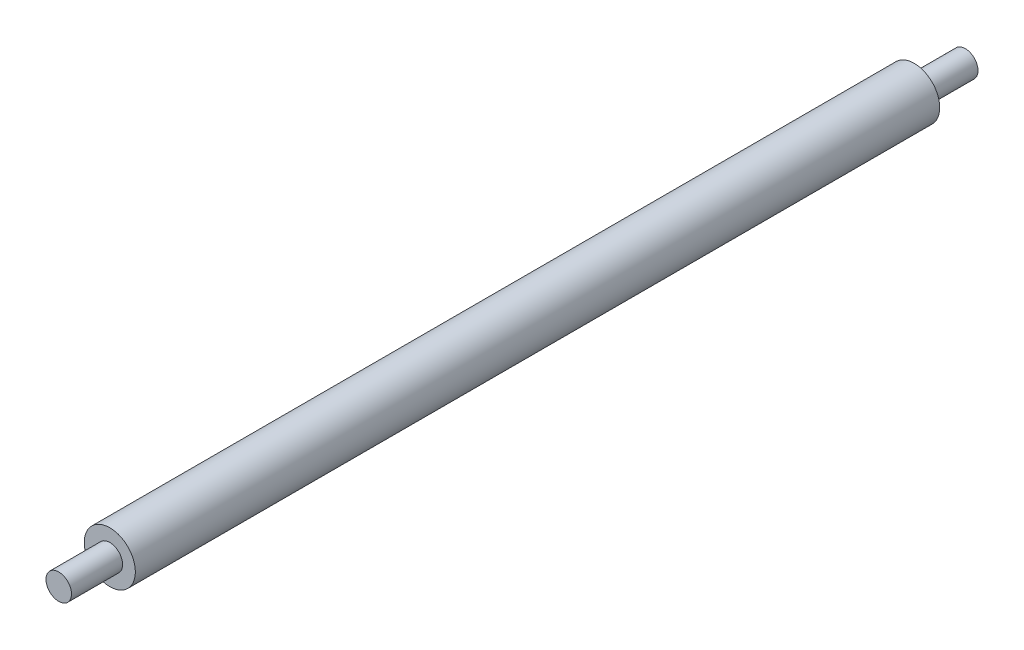
SolidWorks part; units mm, degrees
ref_plane "Front Plane" through (0, 0, 0) normal (0, 0, 1) x (1, 0, 0)
ref_plane "Top Plane" through (0, 0, 0) normal (0, 1, 0) x (1, 0, 0)
ref_plane "Right Plane" through (0, 0, 0) normal (1, 0, 0) x (0, 0, -1)
sketch "Sketch1" plane through (0, 0, 0) normal (0, 0, 1) x (1, 0, 0)
  circle A0 centre (0, 0) radius 10
  dimension "D1" = 20
extrude "Boss-Extrude1" add sketch "Sketch1" along normal blind 315
sketch "Sketch2" plane through (0, 0, 315) normal (0, 0, 1) x (1, 0, 0)
  circle A0 centre (0, 0) radius 5
  dimension "D1" = 10
extrude "Boss-Extrude2" add sketch "Sketch2" along normal blind 20
sketch "Sketch3" plane through (0, 0, 0) normal (0, 0, -1) x (-1, 0, 0)
  circle A0 centre (0, 0) radius 5
  dimension "D1" = 10
extrude "Boss-Extrude3" add sketch "Sketch3" along normal blind 20
